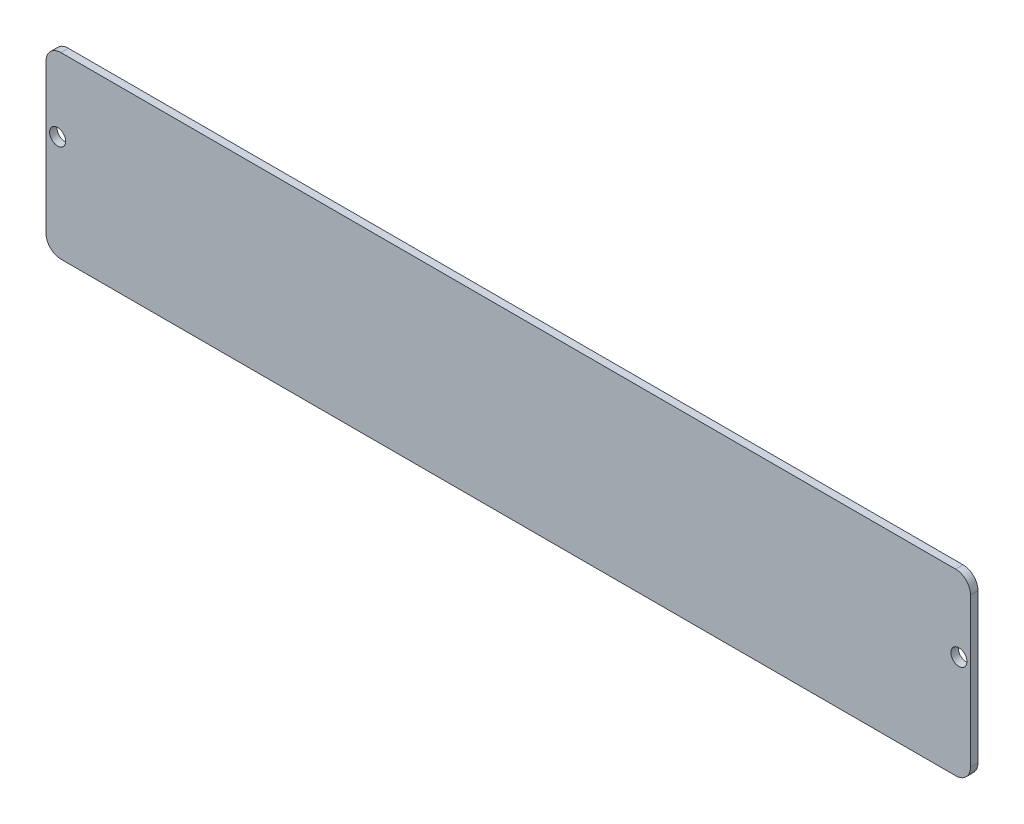
SolidWorks part; units mm, degrees
material "Polyester Resin"
ref_plane "Front Plane" through (0, 0, 0) normal (0, 0, 1) x (1, 0, 0)
ref_plane "Top Plane" through (0, 0, 0) normal (0, 1, 0) x (1, 0, 0)
ref_plane "Right Plane" through (0, 0, 0) normal (1, 0, 0) x (0, 0, -1)
sketch "Sketch1" plane through (0, 0, 0) normal (0, 0, 1) x (1, 0, 0)
  line L2 (-196.85, 69.85) -> (-196.85, 6.35)
  line L3 (-190.5, 0) -> (190.5, 0)
  line L4 (196.85, 69.85) -> (196.85, 6.35)
  line L5 (-190.5, 76.2) -> (190.5, 76.2)
  line L6 (0, -55) -> (0, 55) construction
  arc A8 (196.85, 69.85) -> (190.5, 76.2) centre (190.5, 69.85) ccw
  arc A9 (-196.85, 69.85) -> (-190.5, 76.2) centre (-190.5, 69.85) cw
  arc A10 (190.5, 0) -> (196.85, 6.35) centre (190.5, 6.35) ccw
  arc A11 (-190.5, 0) -> (-196.85, 6.35) centre (-190.5, 6.35) cw
  circle A12 centre (191.897, 44.45) radius 3.429
  circle A13 centre (-191.897, 44.45) radius 3.429
  point P11 (196.85, 0)
  point P26 (196.85, 76.2)
  dimension "D3" = 4.953
  dimension "D4" = 6.858
  dimension "D7" = 6.35
  dimension "D1" = 393.7
  dimension "D2" = 76.2
  dimension "D5" = 31.75
extrude "Boss-Extrude1" add sketch "Sketch1" along normal blind 3.175
